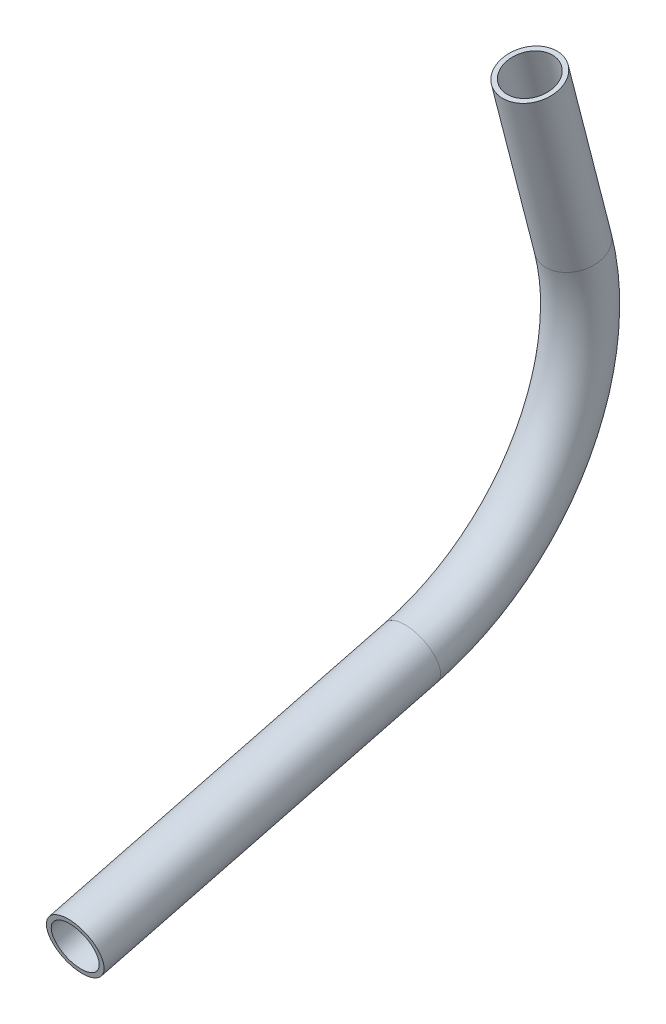
SolidWorks part; units mm, degrees
ref_plane "Front Plane" through (0, 0, 0) normal (0, 0, 1) x (1, 0, 0)
ref_plane "Top Plane" through (0, 0, 0) normal (0, 1, 0) x (1, 0, 0)
ref_plane "Right Plane" through (0, 0, 0) normal (1, 0, 0) x (0, 0, -1)
sketch "Sketch1" plane through (0, 0, 0) normal (1, 0, 0) x (0, 0, -1)
  line L0 (-190.9229, 633.4688) -> (-114.6143, 653.0987)
  line L1 (-78.072, 714.9529) -> (-87.873, 753.0529)
  arc A0 (-114.6143, 653.0987) -> (-78.072, 714.9529) centre (-127.2702, 702.297) ccw
  dimension "D1" = 50.8
  dimension "D2" = 38.1
other "Pipe 0.5 SCH 40(1)"
ref_plane "Plane1" through (0, 633.4688, 190.9229) normal (0, 0.2491, -0.9685) x (0, 0.9685, 0.2491)
sketch "Sketch11" plane through (0, 633.4688, 190.9229) normal (0, 0.2491, -0.9685) x (0, 0.9685, 0.2491)
  circle A0 centre (0, 0) radius 5.2832
  circle A1 centre (0, 0) radius 6.35
  point P5 (0, 0)
  dimension "In_dia" = 10.5664
  dimension "Out_dia" = 12.7
